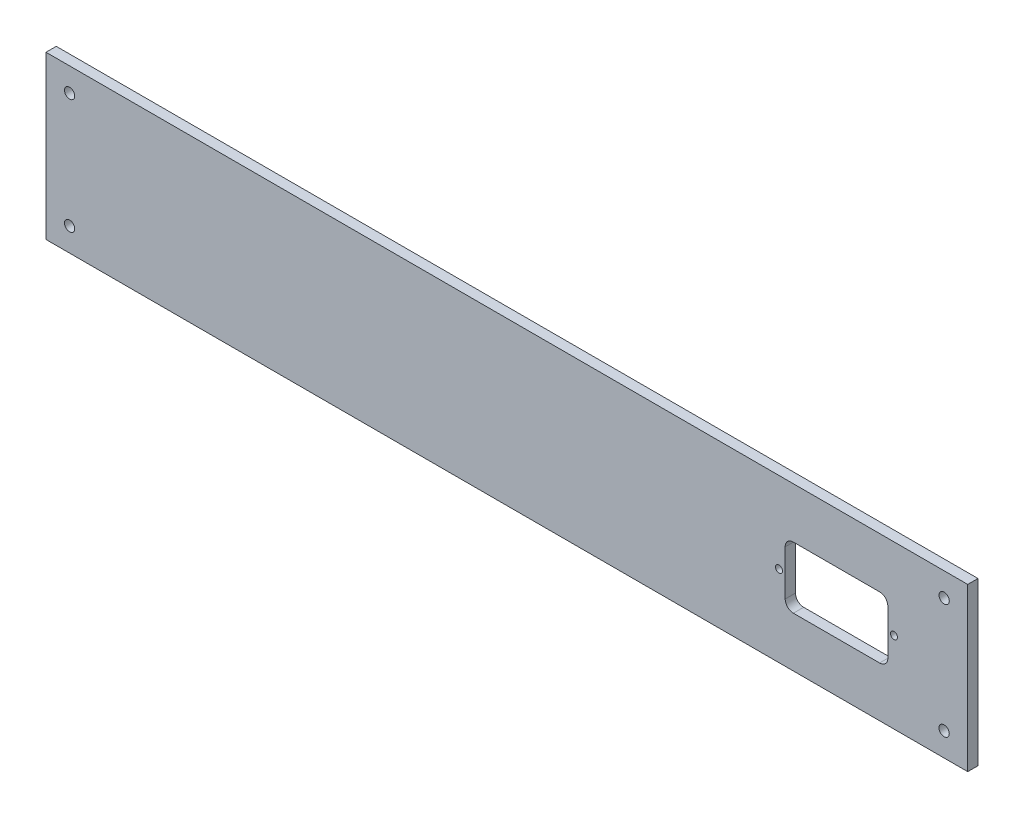
SolidWorks part; units mm, degrees
ref_plane "Piano frontale" through (0, 0, 0) normal (0, 0, 1) x (1, 0, 0)
ref_plane "Piano superiore" through (0, 0, 0) normal (0, 1, 0) x (1, 0, 0)
ref_plane "Piano destro" through (0, 0, 0) normal (1, 0, 0) x (0, 0, -1)
sketch "f" plane through (0, 0, 0) normal (0, 0, 1) x (1, 0, 0)
  line L0 (0, 0) -> (0, 79)
  line L1 (0, 79) -> (449, 79)
  line L2 (449, 79) -> (449, 0)
  line L3 (449, 0) -> (0, 0)
  line L4 (0, 39.5) -> (449, 39.5) construction
  line L5 (224.5, 42) -> (224.5, 123.488) construction
  line L10 (449, 79) -> (224.5, 0) construction
  line L11 (334, 39.5) -> (334, 81.5) construction
  line L12 (224.5, 0) -> (0, 79) construction
  line L13 (112.25, 42) -> (112.25, 84) construction
  circle A0 centre (11.5, 67.5) radius 2.5
  circle A1 centre (437.5, 67.5) radius 2.5
  circle A2 centre (11.5, 11.5) radius 2.5
  circle A3 centre (437.5, 11.5) radius 2.5
  dimension "D3" = 11.5
  dimension "D4" = 11.5
  dimension "D5" = 5
  dimension "D1" = 79
  dimension "D2" = 449
extrude "Estrusione-Estrusione1" add sketch "f" along normal blind 5
sketch "Sketch1" plane through (0, 0, 0) normal (0, 0, -1) x (-1, 0, 0)
  line L0 (0, 39.5) -> (-449, 39.5) construction
  line L1 (0, 79) -> (0, 0) construction
  line L2 (-449, 0) -> (-449, 79) construction
  line L7 (-364.0746, 54.3949) -> (-406.0746, 54.3949)
  line L8 (-360.0746, 50.3949) -> (-360.0746, 28.3949)
  line L9 (-364.0746, 24.3949) -> (-406.0746, 24.3949)
  line L10 (-410.0746, 50.3949) -> (-410.0746, 28.3949)
  arc A4 (-360.0746, 50.3949) -> (-364.0746, 54.3949) centre (-364.0746, 50.3949) ccw
  arc A5 (-360.0746, 28.3949) -> (-364.0746, 24.3949) centre (-364.0746, 28.3949) cw
  arc A6 (-406.0746, 24.3949) -> (-410.0746, 28.3949) centre (-406.0746, 28.3949) cw
  arc A7 (-410.0746, 50.3949) -> (-406.0746, 54.3949) centre (-406.0746, 50.3949) cw
  circle A8 centre (-413.0612, 39.5055) radius 1.7
  circle A9 centre (-357.0612, 39.5055) radius 1.7
extrude "Extrude1" cut sketch "Sketch1" against normal through all
